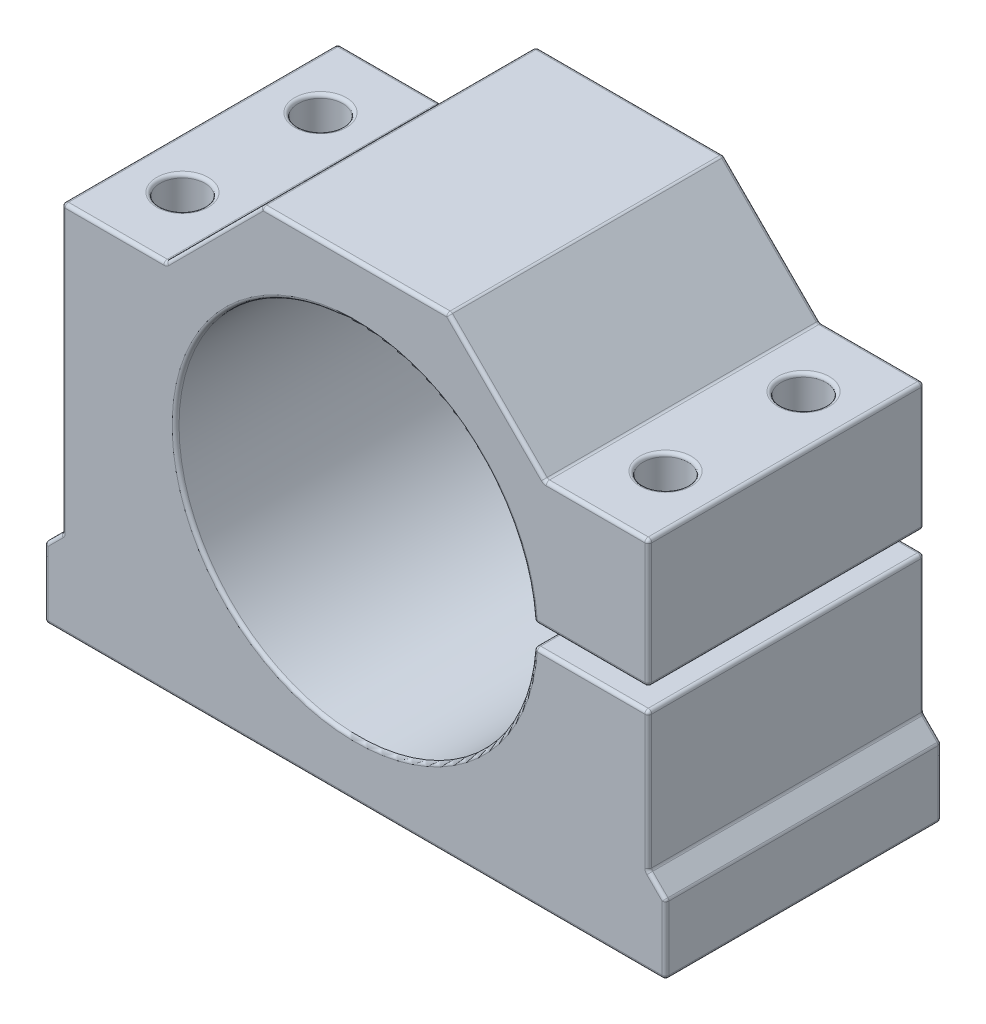
SolidWorks part; units mm, degrees
ref_plane "Front Plane" through (0, 0, 0) normal (0, 0, 1) x (1, 0, 0)
ref_plane "Top Plane" through (0, 0, 0) normal (0, 1, 0) x (1, 0, 0)
ref_plane "Right Plane" through (0, 0, 0) normal (1, 0, 0) x (0, 0, -1)
sketch "Sketch1" plane through (0, 0, 0) normal (0, 0, 1) x (1, 0, 0)
  line L0 (0, 0) -> (0, -34) construction
  line L1 (45, -34) -> (-45, -34)
  line L2 (0, 0) -> (0, 34) construction
  line L3 (13.5, 34) -> (-13.5, 34)
  line L4 (-27.5, 20) -> (-42.5, 20)
  line L5 (-27.5, 20) -> (-13.5, 34)
  line L6 (-45, -34) -> (-45, -24)
  line L7 (-45, -24) -> (-42.5, -21.5)
  line L8 (-42.5, 20) -> (-42.5, -21.5)
  line L9 (45, -34) -> (45, -24)
  line L10 (45, -24) -> (42.5, -21.5)
  line L11 (42.5, 20) -> (42.5, -21.5)
  line L12 (27.5, 20) -> (42.5, 20)
  line L13 (27.5, 20) -> (13.5, 34)
  line L14 (26, 0) -> (42.5, 0) construction
  line L16 (43.25, -1.5) -> (25.25, -1.5)
  line L17 (43.25, -1.5) -> (43.25, 1.5)
  line L18 (43.25, 1.5) -> (25.25, 1.5)
  line L19 (25.25, -1.5) -> (25.25, 1.5)
  line L20 (43.25, -1.5) -> (25.25, 1.5) construction
  line L21 (43.25, 1.5) -> (25.25, -1.5) construction
  circle A0 centre (0, 0) radius 26
  point P19 (34.25, 0)
  dimension "D1" = 52
  dimension "D2" = 34
  dimension "D3" = 45
  dimension "D4" = 34
  dimension "D5" = 13.5
  dimension "D6" = 27.5
  dimension "D7" = 54
  dimension "D8" = 15
  dimension "D9" = 10
  dimension "D10" = 3
  dimension "D11" = 18
extrude "Boss-Extrude1" add sketch "Sketch1" along normal mid plane 40 contours A0 L18 L11 L12 L13 L3 L5 L4 L8 L7 L6 L1 L9 L10 L16
sketch "Sketch2" plane through (0, -34, 0) normal (0, -1, 0) x (1, 0, 0)
  line L0 (0, 20) -> (0, -20) construction
  line L1 (45, 20) -> (-45, 20) construction
  line L2 (45, -20) -> (-45, -20) construction
  circle A0 centre (-35, 10) radius 3.25
  circle A1 centre (-35, -10) radius 3.25
  circle A2 centre (35, -10) radius 3.25
  circle A3 centre (35, 10) radius 3.25
  dimension "D1" = 6.5
  dimension "D2" = 10
  dimension "D3" = 35
  dimension "D5" = 20
  dimension "D4" = 2
extrude "Cut-Extrude1" cut sketch "Sketch2" against normal through all
fillet "Fillet1" radius 0.5 57 edges at (-35, -34, -13.25) (20.5, 27, -20) (0, -34, -20) (-26, 0, -20) (43.75, -22.75, -20) (45, -34, 0) (45, -24, 0) (45, -29, -20) (42.5, -21.5, 0) (42.5, -11.5, -20) (42.5, -11.5, 20) (43.75, -22.75, 20) (45, -29, 20) (0, -34, 20) (20.5, 27, 20) (-26, 0, 20) (25.9567, 1.5, 0) (34.2283, 1.5, 20) (34.2283, 1.5, -20) (38.25, 1.5, -10) (38.25, 1.5, 10) (42.5, -1.5, 0) (34.2283, -1.5, 20) (25.9567, -1.5, 0) (34.2283, -1.5, -20) (38.25, -1.5, -10) (38.25, -1.5, 10) (42.5, 1.5, 0) (42.5, 10.75, 20) (42.5, 10.75, -20) (-45, -29, 20) (-45, -34, 0) (-45, -29, -20) (-43.75, -22.75, 20) (-45, -24, 0) (-43.75, -22.75, -20) (-42.5, -0.75, 20) (-42.5, -21.5, 0) (-42.5, -0.75, -20) (-35, 20, 20) (-42.5, 20, 0) (-35, 20, -20) (-31.75, 20, 10) (-31.75, 20, -10) (-20.5, 27, 20) (-27.5, 20, 0) (-20.5, 27, -20) (13.5, 34, 0) (0, 34, 20) (-13.5, 34, 0) (0, 34, -20) (42.5, 20, 0) (35, 20, 20) (27.5, 20, 0) (35, 20, -20) (31.75, 20, -10) (31.75, 20, 10)
